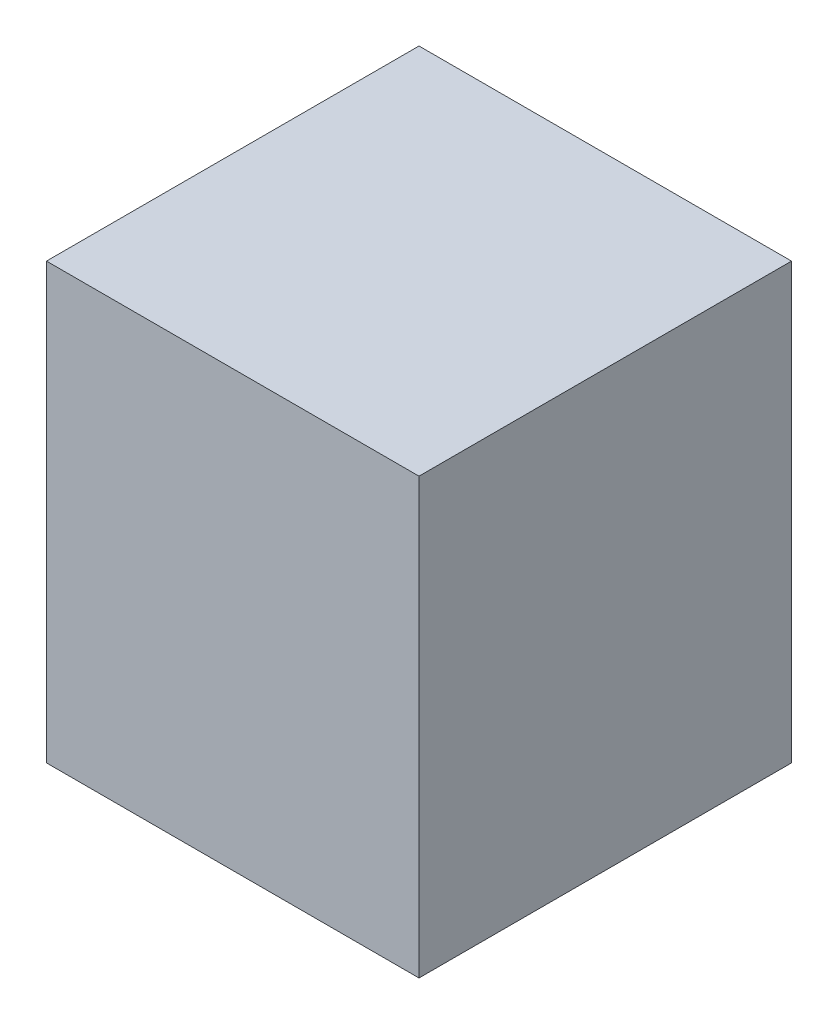
SolidWorks part; units mm, degrees
ref_plane "前视基准面" through (0, 0, 0) normal (0, 0, 1) x (1, 0, 0)
ref_plane "上视基准面" through (0, 0, 0) normal (0, 1, 0) x (1, 0, 0)
ref_plane "右视基准面" through (0, 0, 0) normal (1, 0, 0) x (0, 0, -1)
sketch "草图1" plane through (0, 0, 0) normal (0, 1, 0) x (1, 0, 0)
  line L1 (150, 150) -> (-150, 150)
  line L2 (150, 150) -> (150, -150)
  line L3 (150, -150) -> (-150, -150)
  line L4 (-150, 150) -> (-150, -150)
  line L5 (0, -150) -> (0, 150) construction
  line L6 (150, 0) -> (-150, 0) construction
  point P0 (0, 0)
  dimension "D1" = 300
  dimension "D2" = 300
extrude "凸台-拉伸1" add sketch "草图1" along normal blind 350
